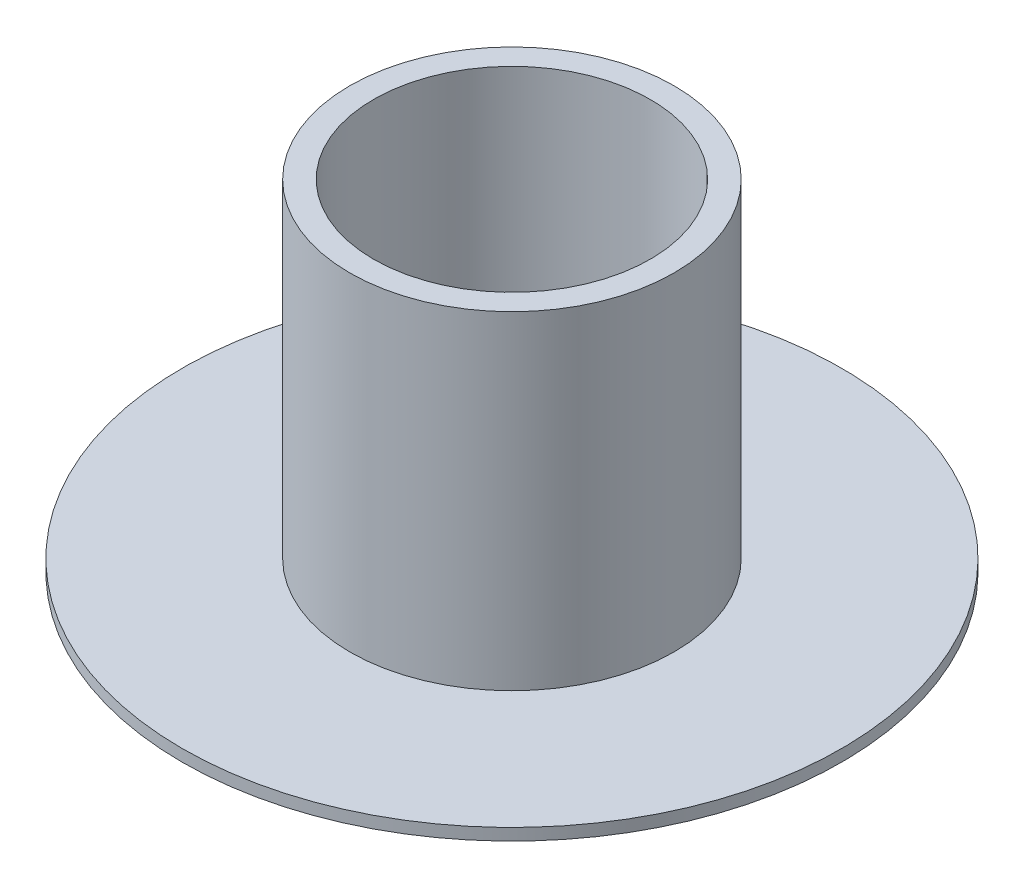
SolidWorks part; units mm, degrees
ref_plane "Alzado" through (0, 0, 0) normal (0, 0, 1) x (1, 0, 0)
ref_plane "Planta" through (0, 0, 0) normal (0, 1, 0) x (1, 0, 0)
ref_plane "Vista lateral" through (0, 0, 0) normal (1, 0, 0) x (0, 0, -1)
sketch "Croquis1" plane through (0, 0, 0) normal (0, 0, 1) x (1, 0, 0)
  line L0 (-39.551, 23.6584) -> (-39.551, -20.2169) construction
  line L1 (-39.551, 1.7207) -> (-50.051, 1.7207) construction
  line L2 (-50.051, 1.7207) -> (-64.551, 1.7207)
  line L3 (-64.551, 1.7207) -> (-64.551, 2.6207)
  line L4 (-64.551, 2.6207) -> (-51.851, 2.6207)
  line L5 (-51.851, 2.6207) -> (-51.851, 27.5207)
  line L6 (-51.851, 27.5207) -> (-50.051, 27.5207)
  line L7 (-50.051, 27.5207) -> (-50.051, 1.7207)
  dimension "D1" = 10.5
  dimension "D2" = 14.5
revolve "Revolución1" add sketch "Croquis1" angle 360 about L0
